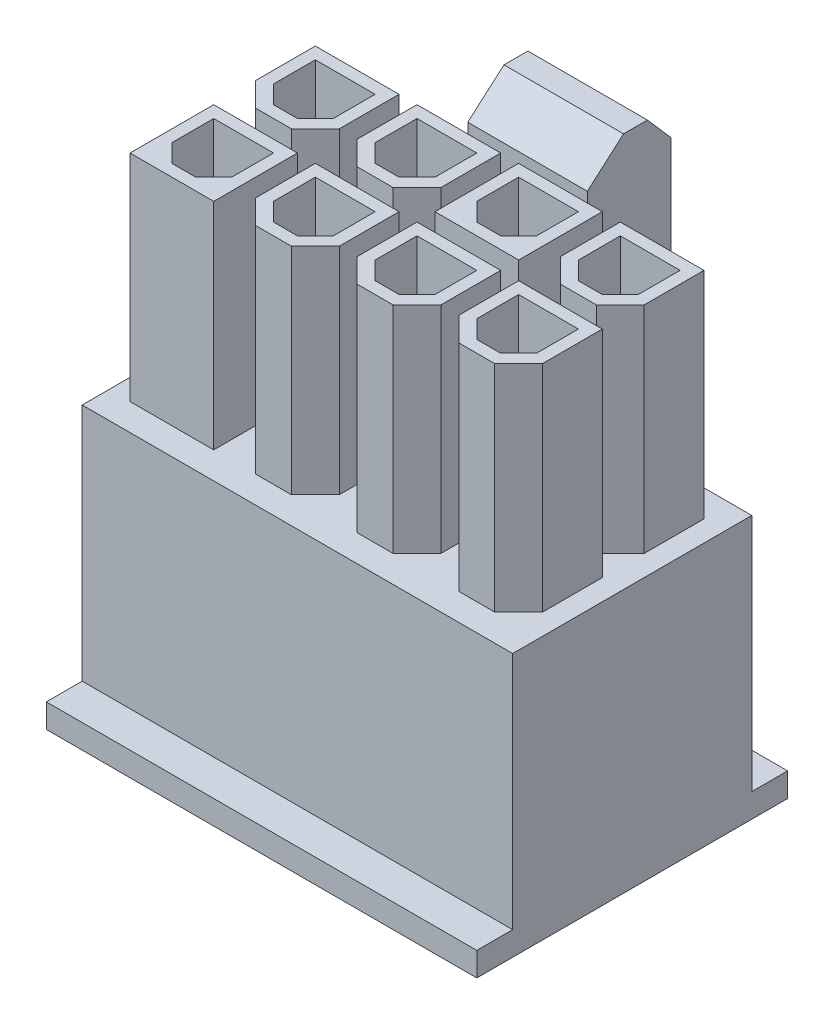
SolidWorks part; units mm, degrees
ref_plane "Ebene vorne" through (0, 0, 0) normal (0, 0, 1) x (1, 0, 0)
ref_plane "Ebene oben" through (0, 0, 0) normal (0, 1, 0) x (1, 0, 0)
ref_plane "Ebene rechts" through (0, 0, 0) normal (1, 0, 0) x (0, 0, -1)
sketch "Skizze1" plane through (0, 0, 0) normal (1, 0, 0) x (0, 0, -1)
  line L1 (5, 0) -> (-5, 0)
  line L2 (5, 0) -> (5, 11)
  line L3 (5, 11) -> (-5, 11)
  line L4 (-5, 0) -> (-5, 11)
  point P4 (0, 0)
  dimension "D1" = 10
  dimension "D2" = 11
extrude "Aufsatz-Linear austragen1" add sketch "Skizze1" along normal mid plane 18
sketch "Skizze2" plane through (0, 0, 0) normal (1, 0, 0) x (0, 0, -1)
  line L0 (0, 0) -> (0, 11) construction
  line L1 (-5, 0) -> (-6.5, 0)
  line L2 (-5, 0) -> (-5, 1)
  line L3 (-5, 1) -> (-6.5, 1)
  line L4 (-6.5, 0) -> (-6.5, 1)
  line L5 (5, 11) -> (-5, 11) construction
  line L6 (6.5, 0) -> (6.5, 1)
  line L7 (5, 1) -> (6.5, 1)
  line L8 (5, 0) -> (5, 1)
  line L9 (5, 0) -> (6.5, 0)
  dimension "D1" = 1.5
  dimension "D2" = 1
extrude "Aufsatz-Linear austragen2" add sketch "Skizze2" along normal mid plane 18
sketch "Skizze3" plane through (0, 0, 0) normal (1, 0, 0) x (0, 0, -1)
  line L0 (5, 11) -> (5.5717, 11)
  line L1 (7.5, 8.198) -> (7.5, 5.198)
  line L2 (7.5, 5.198) -> (8.5, 4)
  line L3 (8.5, 4) -> (8.5, 2)
  line L4 (8.5, 2) -> (6.5, 2)
  line L5 (6.5, 2) -> (6.5, 8)
  line L6 (6.5, 8) -> (5, 8)
  line L7 (5, 1) -> (5, 11) construction
  line L8 (5, 11) -> (5, 8)
  line L9 (-6.5, 0) -> (6.5, 0) construction
  arc A0 (5.5717, 11) -> (6.5359, 9.599) centre (7.0717, 11) ccw
  arc A1 (6.5359, 9.599) -> (7.5, 8.198) centre (6, 8.198) cw
  dimension "D5" = 1.5
  dimension "D1" = 2
  dimension "D2" = 1
  dimension "D3" = 2
  dimension "D4" = 2
  dimension "D6" = 3
  dimension "D7" = 1.5
  dimension "D8" = 3
extrude "Aufsatz-Linear austragen3" add sketch "Skizze3" along normal mid plane 8
sketch "Skizze4" plane through (0, 0, 0) normal (0, -1, 0) x (1, 0, 0)
  line L0 (9, -5) -> (-9, -5) construction
  line L1 (-2.5, -5) -> (2.5, -5)
  line L2 (-2.5, -5) -> (-2.5, -6.5)
  line L3 (-2.5, -6.5) -> (2.5, -6.5)
  line L4 (2.5, -5) -> (2.5, -6.5)
  line L5 (9, -6.5) -> (-9, -6.5) construction
  line L6 (0, -5) -> (0, 0) construction
  line L7 (-4, -6.5) -> (-4, -8.5) construction
  dimension "D1" = 1.5
extrude "Schnitt-Linear austragen1" cut sketch "Skizze4" against normal through all
sketch "Skizze5" plane through (0, 0, 0) normal (1, 0, 0) x (0, 0, -1)
  line L0 (8.1235, 4.451) -> (8.1235, 19.8707)
  line L1 (8.5, 4) -> (7.5, 5.198) construction
  line L2 (8.1235, 19.8707) -> (7.1363, 21)
  line L3 (7.1363, 21) -> (6.1363, 21)
  line L4 (6.1363, 21) -> (4.6235, 19.6776)
  line L5 (4.6235, 19.6776) -> (4.6235, 17.6776)
  line L6 (4.6235, 17.6776) -> (6.1235, 17.6776)
  line L7 (6.1235, 17.6776) -> (6.5, 8)
  line L8 (6.5, 8) -> (6.5, 2)
  line L9 (6.5, 2) -> (8.1235, 4.451)
  line L10 (5, 11) -> (-5, 11) construction
  dimension "D1" = 3.5
  dimension "D2" = 1.5
  dimension "D3" = 1
  dimension "D4" = 10
  dimension "D5" = 2
  dimension "D6" = 2.0093
  dimension "D7" = 1.5
extrude "Aufsatz-Linear austragen4" add sketch "Skizze5" along normal mid plane 5
sketch "Skizze6" plane through (0, 0, 0) normal (0, -1, 0) x (1, 0, 0)
  line L0 (-9, 6.5) -> (-9, -6.5) construction
  line L1 (-8.25, -4) -> (-4.5, -4)
  line L2 (-8.25, -4) -> (-8.25, -0.25)
  line L3 (-8.25, -0.25) -> (-4.5, -0.25)
  line L4 (-4.5, -4) -> (-4.5, -0.25)
  line L5 (-2.5, -5) -> (-9, -5) construction
  dimension "D1" = 0.75
  dimension "D2" = 1
  dimension "D3" = 3.75
extrude "Schnitt-Linear austragen2" cut sketch "Skizze6" against normal blind 10
pattern_linear "Lineares Muster1" count 4 spacing 4.25 along (1, 0, 0) count 2 spacing 4.25 along (0, 0, 1) of "Schnitt-Linear austragen2"
sketch "Skizze7" plane through (0, 11, 0) normal (0, 1, 0) x (1, 0, 0)
  line L1 (-4.5, -0.25) -> (-8.25, -4) construction
  line L2 (-8.25, -0.25) -> (-4.5, -4) construction
  line L4 (-8.125, -0.375) -> (-4.625, -0.375)
  line L6 (-8.125, -0.375) -> (-8.125, -3.875)
  line L8 (-8.125, -3.875) -> (-4.625, -3.875)
  line L10 (-4.625, -0.375) -> (-4.625, -3.875)
  line L11 (-8.125, -0.375) -> (-4.625, -3.875) construction
  point P4 (-6.375, -2.125)
  dimension "D1" = 3.5
extrude "Aufsatz-Linear austragen5" add sketch "Skizze7" along normal blind 9
pattern_linear "Lineares Muster2" count 3 spacing 4.25 along (1, 0, 0) count 2 spacing 4.25 along (0, 0, 1) of "Aufsatz-Linear austragen5"
sketch "Skizze10" plane through (0, 11, 0) normal (0, 1, 0) x (1, 0, 0)
  line L0 (-8.25, 4) -> (-4.5, 0.25) construction
  line L1 (-4.5, 4) -> (-8.25, 0.25) construction
  line L3 (-4.625, 1.375) -> (-5.625, 0.375)
  line L5 (-5.625, 0.375) -> (-7.125, 0.375)
  line L6 (-4.625, 1.375) -> (-4.625, 3.875)
  line L7 (-4.625, 3.875) -> (-8.125, 3.875)
  line L8 (-8.125, 1.375) -> (-8.125, 3.875)
  line L9 (-4.625, 0.375) -> (-8.125, 3.875) construction
  line L10 (-4.625, 3.875) -> (-8.125, 0.375) construction
  line L11 (-7.125, 0.375) -> (-8.125, 1.375)
  point P4 (-6.375, 2.125)
  dimension "D1" = 3.5
extrude "Aufsatz-Linear austragen7" add sketch "Skizze10" along normal up to surface (9 mm away) up to face at (-6.375, 20, 2.125)
pattern_linear "Lineares Muster4" count 4 spacing 4.25 along (1, 0, 0) count 2 spacing 4.25 along (0, 0, 1) skipping (0, 1), (2, 0) of "Aufsatz-Linear austragen7"
sketch "Skizze12" plane through (0, 20, 0) normal (0, 1, 0) x (1, 0, 0)
  line L16 (-8.25, 2.125) -> (-4.5, 2.125) construction
  line L17 (-6.375, 4) -> (-6.375, 0.25) construction
  line L18 (-8.25, 4) -> (-3.0668, -1.1832) construction
  line L19 (-5.875, 0.875) -> (-5.125, 1.625)
  line L20 (-7.625, 3.375) -> (-5.125, 3.375)
  line L21 (-7.625, 3.375) -> (-7.625, 1.625)
  line L22 (-6.875, 0.875) -> (-5.875, 0.875)
  line L23 (-5.125, 3.375) -> (-5.125, 1.625)
  line L24 (-7.625, 3.375) -> (-5.125, 0.875) construction
  line L25 (-7.625, 0.875) -> (-5.125, 3.375) construction
  line L26 (-7.625, 1.625) -> (-6.875, 0.875)
  line L27 (-4.5, 4) -> (-4.5, 0.25) construction
  line L28 (-8.25, 0.25) -> (-8.25, 4) construction
  line L29 (-8.25, 4) -> (-4.5, 4) construction
  line L30 (-4.5, 0.25) -> (-8.25, 0.25) construction
  point P35 (-6.375, 2.125)
  dimension "D1" = 2.5
  dimension "D3" = 0.75
  dimension "D4" = 0.75
  dimension "D5" = 0.75
  dimension "D6" = 0.75
  dimension "D7" = 2.5
extrude "Schnitt-Linear austragen4" cut sketch "Skizze12" against normal through all
pattern_linear "Lineares Muster6" count 4 spacing 4.25 along (1, 0, 0) count 2 spacing 4.25 along (0, 0, 1) of "Schnitt-Linear austragen4"
